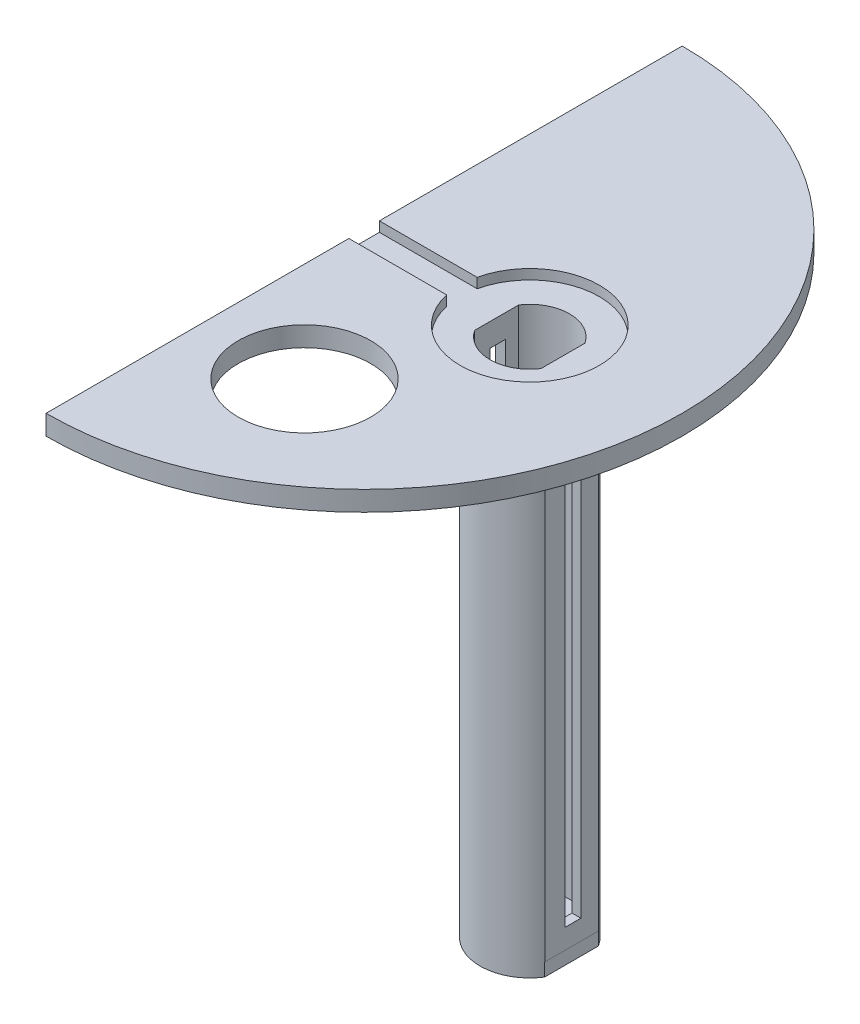
SolidWorks part; units mm, degrees
ref_plane "Front Plane" through (0, 0, 0) normal (0, 0, 1) x (1, 0, 0)
ref_plane "Top Plane" through (0, 0, 0) normal (0, 1, 0) x (1, 0, 0)
ref_plane "Right Plane" through (0, 0, 0) normal (1, 0, 0) x (0, 0, -1)
sketch "Sketch2" plane through (0, 0, 0) normal (0, 1, 0) x (1, 0, 0)
  line L0 (0, 48) -> (0, -48)
  line L2 (25, 28.5186) -> (25, -36.9052) construction
  line L3 (0, 0) -> (59.2697, 0) construction
  arc A0 (0, -48) -> (0, 48) centre (0, 0) ccw
  dimension "D1" = 96
  dimension "D4" = 25
extrude "Boss-Extrude2" add sketch "Sketch2" along normal blind 3
sketch "Sketch3" plane through (0, 3, 0) normal (0, 1, 0) x (1, 0, 0)
  line L0 (0, 0) -> (69.5275, 0) construction
  line L1 (0, 48) -> (0, -48) construction
  line L2 (25, 50.5932) -> (25, -54.3924) construction
  line L3 (14.755, 2.3) -> (0, 2.3)
  line L4 (14.755, -2.3) -> (0, -2.3)
  line L5 (0, 2.3) -> (0, -2.3)
  arc A0 (14.755, -2.3) -> (14.755, 2.3) centre (25, 0) ccw
  dimension "D2" = 21
  dimension "D1" = 25
  dimension "D3" = 2.3
  dimension "D4" = 2.3
extrude "Cut-Extrude1" cut sketch "Sketch3" against normal blind 1.5
sketch "Sketch4" plane through (0, 1.5, 0) normal (0, 1, 0) x (1, 0, 0)
  line L0 (20, 3.3166) -> (20, -3.3166)
  line L1 (30, 3.3166) -> (30, -3.3166)
  arc A0 (20, -3.3166) -> (30, -3.3166) centre (25, 0) ccw
  arc A1 (30, 3.3166) -> (20, 3.3166) centre (25, 0) ccw
  dimension "D1" = 12
  dimension "D2" = 5
  dimension "D3" = 5
extrude "Cut-Extrude4" cut sketch "Sketch4" against normal blind 4
sketch "Sketch6" plane through (0, 0, 0) normal (0, -1, 0) x (1, 0, 0)
  line L0 (20, 3.3166) -> (20, -3.3166)
  line L1 (20, -3.3166) -> (20, 3.3166) construction
  line L4 (18.4235, 3.6056) -> (18.4235, -3.6056)
  line L5 (31.3391, 4.0083) -> (31.3391, -4.0083)
  line L6 (20, 3.3166) -> (20, -3.3166)
  line L7 (30, 3.3166) -> (30, -3.3166)
  arc A0 (30, 3.3166) -> (20, 3.3166) centre (25, 0) ccw
  arc A1 (18.4235, -3.6056) -> (31.3391, -4.0083) centre (25, 0) ccw
  arc A2 (20, -3.3166) -> (30, -3.3166) centre (25, 0) ccw
  arc A3 (31.3391, 4.0083) -> (18.4235, 3.6056) centre (25, 0) ccw
  dimension "D1" = 12
  dimension "D2" = 15
  dimension "D3" = 5
  dimension "D4" = 5
extrude "Boss-Extrude4" add sketch "Sketch6" along normal blind 75
sketch "Sketch8" plane through (0, -75, 0) normal (0, -1, 0) x (1, 0, 0)
  line L0 (18.4, 3.5623) -> (18.4, -3.5623)
  line L1 (31.3, 4.0694) -> (31.3, -4.0694)
  arc A0 (18.4, -3.5623) -> (31.3, -4.0694) centre (25, 0) ccw
  arc A1 (31.3, 4.0694) -> (18.4, 3.5623) centre (25, 0) ccw
  dimension "D1" = 15
  dimension "D2" = 6.6
  dimension "D3" = 6.3
extrude "Boss-Extrude6" add sketch "Sketch8" along normal blind 2
sketch "Sketch9" plane through (18.4235, 0, 0) normal (-1, 0, 0) x (0, 0, 1)
  line L0 (-1.3702, -2) -> (1.0298, -2)
  line L1 (1.0298, -2) -> (1.0298, -72)
  line L2 (1.0298, -72) -> (-1.3702, -72)
  line L3 (-1.3702, -72) -> (-1.3702, -2)
  line L4 (3.5623, -77) -> (-3.5623, -77) construction
  dimension "D1" = 5
  dimension "D2" = 70
  dimension "D3" = 2.4
extrude "Cut-Extrude5" cut sketch "Sketch9" against normal blind 20
sketch "Sketch11" plane through (0, 3, 0) normal (0, 1, 0) x (1, 0, 0)
  line L0 (0, -2.3) -> (0, -48) construction
  circle A0 centre (15, -24) radius 10
  dimension "D1" = 20
  dimension "D2" = 15
  dimension "D3" = 24
extrude "Cut-Extrude6" cut sketch "Sketch11" against normal blind 4
